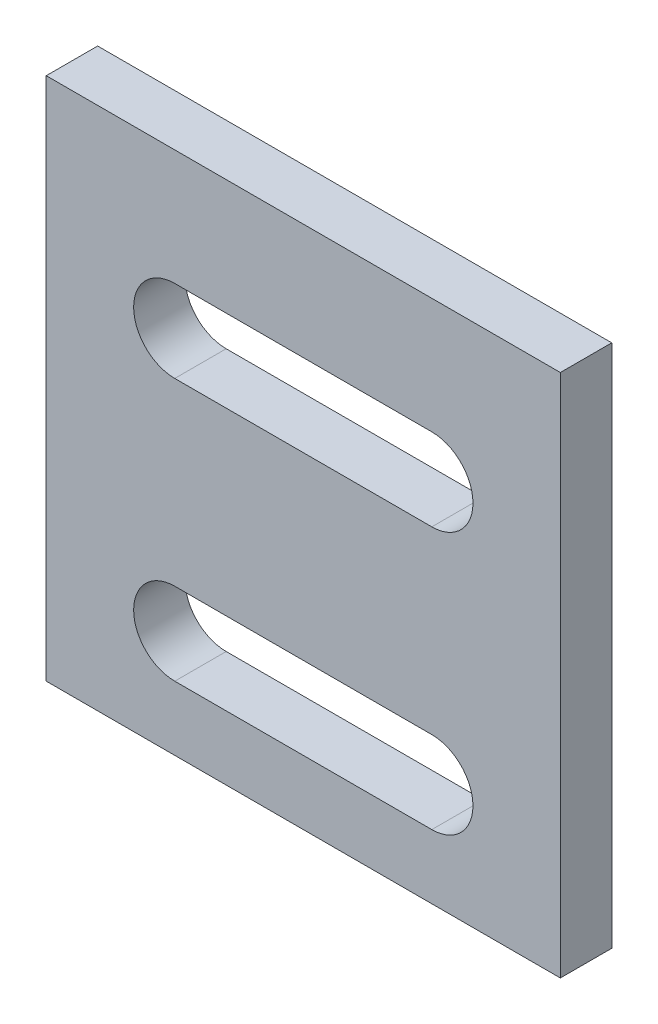
SolidWorks part; units mm, degrees
material "Thornel Mat VMA"
ref_plane "前视基准面" through (0, 0, 0) normal (0, 0, 1) x (1, 0, 0)
ref_plane "上视基准面" through (0, 0, 0) normal (0, 1, 0) x (1, 0, 0)
ref_plane "右视基准面" through (0, 0, 0) normal (1, 0, 0) x (0, 0, -1)
other "Configuration Table"
sketch "草图1" plane through (0, 0, 0) normal (0, 0, 1) x (1, 0, 0)
  line L0 (1.8245, 7.8397) -> (-18.1755, 7.8397) construction
  line L1 (-18.1755, 18.0397) -> (1.8245, 18.0397)
  line L2 (-18.1755, 18.0397) -> (-18.1755, -2.3603)
  line L3 (-18.1755, -2.3603) -> (1.8245, -2.3603)
  line L4 (1.8245, 18.0397) -> (1.8245, -2.3603)
  line L5 (-8.1755, 18.0397) -> (-8.1755, 7.8397) construction
  line L6 (-8.1755, 7.8397) -> (-8.1755, -2.3603) construction
  line L8 (1.8245, 11.9397) -> (-18.1755, 11.9397) construction
  line L9 (-13.1755, 11.9397) -> (-3.1755, 11.9397) construction
  line L10 (-13.1755, 13.5397) -> (-3.1755, 13.5397)
  line L11 (-13.1755, 10.3397) -> (-3.1755, 10.3397)
  line L12 (-13.1755, 1.7397) -> (-3.1755, 1.7397) construction
  line L13 (-13.1755, 0.1397) -> (-3.1755, 0.1397)
  line L14 (-13.1755, 3.3397) -> (-3.1755, 3.3397)
  arc A0 (-13.1755, 13.5397) -> (-13.1755, 10.3397) centre (-13.1755, 11.9397) ccw
  arc A1 (-3.1755, 10.3397) -> (-3.1755, 13.5397) centre (-3.1755, 11.9397) ccw
  arc A2 (-13.1755, 0.1397) -> (-13.1755, 3.3397) centre (-13.1755, 1.7397) cw
  arc A3 (-3.1755, 3.3397) -> (-3.1755, 0.1397) centre (-3.1755, 1.7397) cw
  point P8 (0, 0)
  point P10 (0, 0)
  point P13 (-8.1755, 7.8397)
  point P16 (-8.1755, 11.9397)
  point P23 (-8.1755, 1.7397)
  point P28 (0, 0)
  dimension "D4" = 1.6
  dimension "D1" = 1.6
  dimension "D2" = 20
  dimension "D3" = 20.4
  dimension "D5" = 10
  dimension "D6" = 10
  dimension "D7" = 6.1
  dimension "D8" = 4.1
extrude "凸台-拉伸1" add sketch "草图1" along normal blind 2 contours L2 L1 L4 L3
